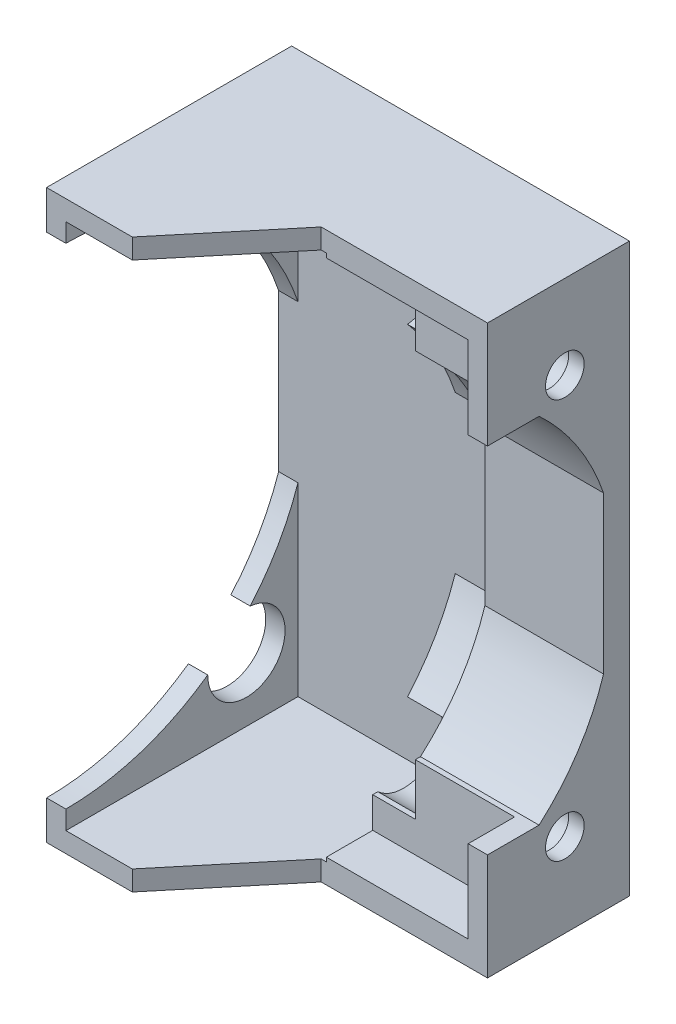
SolidWorks part; units mm, degrees
ref_plane "Alzado" through (0, 0, 0) normal (0, 0, 1) x (1, 0, 0)
ref_plane "Planta" through (0, 0, 0) normal (0, 1, 0) x (1, 0, 0)
ref_plane "Vista lateral" through (0, 0, 0) normal (1, 0, 0) x (0, 0, -1)
sketch "Croquis1" plane through (0, 0, 0) normal (0, 0, 1) x (1, 0, 0)
  line L1 (-34.6141, 8.9096) -> (-9.6141, 8.9096)
  line L2 (-34.6141, 8.9096) -> (-34.6141, -35.0904)
  line L3 (-34.6141, -35.0904) -> (-9.6141, -35.0904)
  line L4 (-9.6141, 8.9096) -> (-9.6141, -35.0904)
  dimension "D1" = 25
  dimension "D2" = 44
extrude "Saliente-Extruir1" add sketch "Croquis1" along normal blind 20
sketch "Croquis2" plane through (0, 0, 20) normal (0, 0, 1) x (1, 0, 0)
  line L0 (-34.6141, 8.9096) -> (-34.6141, -35.0904) construction
  line L1 (-32.6141, 7.1096) -> (-21.3141, 7.1096)
  line L2 (-32.6141, 7.1096) -> (-32.6141, -33.2904)
  line L3 (-32.6141, -33.2904) -> (-21.3141, -33.2904)
  line L4 (-21.3141, 7.1096) -> (-21.3141, -33.2904)
  line L5 (-9.6141, 8.9096) -> (-34.6141, 8.9096) construction
  dimension "D1" = 2
  dimension "D2" = 11.3
  dimension "D3" = 1.8
  dimension "D4" = 40.4
extrude "Cortar-Extruir1" cut sketch "Croquis2" against normal blind 18
sketch "Croquis3" plane through (0, 0, 20) normal (0, 0, 1) x (1, 0, 0)
  line L0 (-34.6141, -35.0904) -> (-9.6141, -35.0904) construction
  line L1 (-9.6141, 8.9096) -> (-20.3141, 8.9096)
  line L2 (-9.6141, 8.9096) -> (-9.6141, -35.0904)
  line L3 (-9.6141, -35.0904) -> (-20.3141, -35.0904)
  line L4 (-20.3141, 8.9096) -> (-20.3141, -35.0904)
  line L5 (-21.3141, -33.2904) -> (-21.3141, 7.1096) construction
  dimension "D1" = 1
extrude "Cortar-Extruir2" cut sketch "Croquis3" against normal blind 12
sketch "Croquis4" plane through (-34.6141, 0, 0) normal (-1, 0, 0) x (0, 0, 1)
  line L1 (20, 5.9096) -> (20, -32.0904)
  line L2 (0, 8.9096) -> (0, -35.0904) construction
  line L5 (20, 8.9096) -> (0, 8.9096) construction
  circle A0 centre (6, 2.4096) radius 1.6
  arc A1 (20, 5.9096) -> (20, -32.0904) centre (20, -13.0904) ccw
  circle A2 centre (6, -28.5904) radius 1.6
  dimension "D1" = 6
  dimension "D3" = 31
  dimension "D2" = 6.5
  dimension "D4" = 6
extrude "Cortar-Extruir3" cut sketch "Croquis4" against normal up to vertex
sketch "Croquis5" plane through (-34.6141, 0, 0) normal (-1, 0, 0) x (0, 0, 1)
  circle A0 centre (6, 2.4096) radius 3
  circle A1 centre (6, -28.5904) radius 3
extrude "Cortar-Extruir4" cut sketch "Croquis5" against normal blind 17
sketch "Croquis7" plane through (0, 0, 8) normal (0, 0, 1) x (1, 0, 0)
  line L0 (-20.3141, -30.8265) -> (-20.3141, -35.0904) construction
  line L1 (-9.6141, -35.0904) -> (-20.3141, -35.0904)
  line L2 (-9.6141, -35.0904) -> (-9.6141, -32.9585)
  line L3 (-9.6141, -32.9585) -> (-20.3141, -32.9585)
  line L4 (-20.3141, -35.0904) -> (-20.3141, -32.9585)
  line L5 (-20.3141, 8.9096) -> (-20.3141, 4.6456) construction
  line L6 (-9.6141, 8.9096) -> (-20.3141, 8.9096)
  line L7 (-9.6141, 8.9096) -> (-9.6141, 6.7776)
  line L8 (-9.6141, 6.7776) -> (-20.3141, 6.7776)
  line L9 (-20.3141, 8.9096) -> (-20.3141, 6.7776)
extrude "Saliente-Extruir2" add sketch "Croquis7" along normal up to vertex (12 mm away)
sketch "Croquis9" plane through (0, 0, 2) normal (0, 0, 1) x (1, 0, 0)
  line L1 (-21.3141, -7.0077) -> (-32.6141, -7.0077)
  line L2 (-21.3141, -7.0077) -> (-21.3141, -19.1732)
  line L3 (-21.3141, -19.1732) -> (-32.6141, -19.1732)
  line L4 (-32.6141, -7.0077) -> (-32.6141, -19.1732)
extrude "Saliente-Extruir3" add sketch "Croquis9" against normal up to vertex (2 mm away)
sketch "Croquis11" plane through (-32.6141, 0, 0) normal (-1, 0, 0) x (0, 0, 1)
  line L0 (2, -7.0077) -> (2, -19.1732)
  arc A0 (2, -7.0077) -> (2, -19.1732) centre (20, -13.0904) ccw
extrude "Saliente-Extruir4" add sketch "Croquis11" along normal up to vertex (2 mm away)
sketch "Croquis12" plane through (-34.6141, 0, 0) normal (-1, 0, 0) x (0, 0, 1)
  line L0 (20, -35.0904) -> (0, -35.0904) construction
  line L1 (0, 8.9096) -> (0.99, 8.9096)
  line L2 (0, 8.9096) -> (0, -35.0904)
  line L3 (0, -35.0904) -> (0.99, -35.0904)
  line L4 (0.99, 8.9096) -> (0.99, -35.0904)
  dimension "D1" = 0.99
extrude "Cortar-Extruir10" cut sketch "Croquis12" against normal up to vertex
sketch "Croquis13" plane through (-9.6141, 0, 0) normal (1, 0, 0) x (0, 0, -1)
  line L0 (-20, 8.9096) -> (-0.99, 8.9096) construction
  line L1 (-20, -35.0904) -> (-12, -35.0904)
  line L2 (-20, -35.0904) -> (-20, 8.9096)
  line L3 (-20, 8.9096) -> (-12, 8.9096)
  line L4 (-12, -35.0904) -> (-12, 8.9096)
  dimension "D1" = 8
extrude "Cortar-Extruir11" cut sketch "Croquis13" against normal up to vertex (11.7 mm away)
sketch "Croquis14" plane through (-21.3141, 0, 0) normal (1, 0, 0) x (0, 0, -1)
  line L0 (-2, -19.1732) -> (-2, -7.0077)
  arc A0 (-2, -19.1732) -> (-2, -7.0077) centre (-20, -13.0904) ccw
extrude "Saliente-Extruir5" add sketch "Croquis14" along normal up to vertex (11.7 mm away)
sketch "Croquis15" plane through (0, 0, 12) normal (0, 0, 1) x (1, 0, 0)
  line L1 (-9.6141, 6.7776) -> (-9.6141, 8.9096) construction
  line L2 (-20.3777, -33.4585) -> (-9.6141, -33.4585)
  line L3 (-20.3777, -33.4585) -> (-20.3777, 7.2776)
  line L4 (-20.3777, 7.2776) -> (-9.6141, 7.2776)
  line L8 (-9.6141, -33.4585) -> (-9.6141, 7.2776)
  line L9 (-20.3141, -32.9585) -> (-9.6141, -32.9585) construction
  line L10 (-9.6141, 6.7776) -> (-20.3141, 6.7776) construction
  dimension "D1" = 0.5
  dimension "D2" = 0.5
extrude "Cortar-Extruir12" cut sketch "Croquis15" against normal up to vertex (4 mm away)
sketch "Croquis16" plane through (-9.6141, 0, 0) normal (1, 0, 0) x (0, 0, -1)
  line L0 (-8, -27.8213) -> (-8, -33.4585)
  line L1 (-8, -33.4585) -> (-12, -33.4585)
  line L2 (-12, -33.4585) -> (-12, -35.0904)
  line L3 (-12, -35.0904) -> (-0.99, -35.0904)
  line L4 (-0.99, -35.0904) -> (-0.99, 8.9096)
  line L5 (-0.99, -35.0904) -> (-0.99, 8.9096) construction
  line L6 (-2, -7.0077) -> (-2, -19.1732)
  line L7 (-2, -7.0077) -> (-2, -19.1732) construction
  line L8 (-2, -13.0904) -> (-0.99, -13.0904) construction
  line L9 (-12, 8.9096) -> (-0.99, 8.9096)
  line L10 (-12, 7.2776) -> (-12, 8.9096)
  line L11 (-8, 7.2776) -> (-12, 7.2776)
  line L12 (-8, 1.6405) -> (-8, 7.2776)
  arc A0 (-8, -27.8213) -> (-2, -19.1732) centre (-20, -13.0904) ccw
  arc A1 (-8, 1.6405) -> (-2, -7.0077) centre (-20, -13.0904) cw
  circle A2 centre (-6, -28.5904) radius 1.5
  circle A3 centre (-6, 2.4096) radius 1.5
extrude "Saliente-Extruir6" add sketch "Croquis16" along normal blind 1.2
sketch "Croquis17" plane through (0, -35.0904, 0) normal (0, -1, 0) x (1, 0, 0)
  line L0 (-21.3141, 12) -> (-21.3141, 20)
  line L1 (-21.3141, 20) -> (-27.9641, 20)
  line L2 (-34.6141, 20) -> (-21.3141, 20) construction
  line L3 (-27.9641, 20) -> (-21.3141, 12)
extrude "Cortar-Extruir13" cut sketch "Croquis17" against normal up to vertex
sketch "Croquis18" plane through (0, 0, 12) normal (0, 0, 1) x (1, 0, 0)
  line L2 (-20.3777, 7.2776) -> (-21.3141, 7.2776)
  line L3 (-20.3777, 7.2776) -> (-20.3777, -33.2904)
  line L4 (-20.3777, -33.2904) -> (-21.3141, -33.2904)
  line L5 (-21.3141, 7.2776) -> (-21.3141, -33.2904)
extrude "Cortar-Extruir14" cut sketch "Croquis18" against normal up to vertex (4 mm away)
sketch "Croquis19" plane through (-8.4141, 0, 0) normal (1, 0, 0) x (0, 0, -1)
  line L0 (-2, -19.1732) -> (-2, -7.0077)
  line L1 (-8, -27.8213) -> (-8, -26.8213)
  line L2 (-8, 1.6405) -> (-8, 0.6405)
  line L3 (-3, -19.1732) -> (-3, -7.0077)
  arc A0 (-2, -19.1732) -> (-8, -27.8213) centre (-20, -13.0904) cw
  arc A1 (-2, -7.0077) -> (-8, 1.6405) centre (-20, -13.0904) ccw
  arc A2 (-8, -26.8213) -> (-3, -19.1732) centre (-19.1028, -14.1044) ccw
  arc A3 (-8, 0.6405) -> (-3, -7.0077) centre (-20.7177, -13.1322) cw
  dimension "D1" = 1
  dimension "D3" = 1
  dimension "D4" = 12.1655
  dimension "D5" = 1
extrude "Saliente-Extruir7" add sketch "Croquis19" against normal up to vertex
sketch "Croquis20" plane through (-8.4141, 0, 0) normal (1, 0, 0) x (0, 0, -1)
  line L1 (-8, -33.4585) -> (-12, -33.4585)
  line L2 (-8, -33.4585) -> (-8, -33.2224)
  line L3 (-8, -33.2224) -> (-12, -33.2224)
  line L4 (-12, -33.4585) -> (-12, -33.2224)
  line L5 (-8, 7.2776) -> (-12, 7.2776)
  line L6 (-8, 7.2776) -> (-8, 7.0276)
  line L7 (-8, 7.0276) -> (-12, 7.0276)
  line L8 (-12, 7.2776) -> (-12, 7.0276)
  dimension "D1" = 0.25
  dimension "D2" = 40.25
extrude "Saliente-Extruir8" add sketch "Croquis20" against normal up to vertex
sketch "Croquis21" plane through (-8.4141, 0, 0) normal (1, 0, 0) x (0, 0, -1)
  line L1 (-12, -33.2224) -> (-8, -33.2224)
  line L2 (-12, -33.2224) -> (-12, -26.8213)
  line L3 (-12, -26.8213) -> (-8, -26.8213)
  line L4 (-8, -33.2224) -> (-8, -26.8213)
  line L5 (-8, 0.6405) -> (-12, 0.6405)
  line L6 (-8, 0.6405) -> (-8, 7.0276)
  line L7 (-8, 7.0276) -> (-12, 7.0276)
  line L8 (-12, 0.6405) -> (-12, 7.0276)
extrude "Saliente-Extruir9" add sketch "Croquis21" against normal blind 1.5
sketch "Croquis22" plane through (0, 0, 8) normal (0, 0, 1) x (1, 0, 0)
  line L0 (-9.9141, 7.0276) -> (-21.3141, 7.0276)
  line L1 (-21.3141, 7.0276) -> (-21.3141, 4.6456)
  line L2 (-21.3141, 4.6456) -> (-17.6141, 4.6456)
  line L3 (-17.6141, 4.6456) -> (-17.6141, 0.6405)
  line L4 (-17.6141, 0.6405) -> (-9.9141, 0.6405)
  line L5 (-9.9141, 0.6405) -> (-9.9141, 7.0276)
  line L6 (-9.9141, -26.8213) -> (-17.6141, -26.8213)
  line L7 (-17.6141, -26.8213) -> (-17.6141, -30.8265)
  line L8 (-17.6141, -30.8265) -> (-21.3141, -30.8265)
  line L9 (-21.3141, -30.8265) -> (-21.3141, -33.2224)
  line L10 (-21.3141, -33.2224) -> (-9.9141, -33.2224)
  line L11 (-9.9141, -33.2224) -> (-9.9141, -26.8213)
extrude "Saliente-Extruir10" add sketch "Croquis22" along normal blind 0.4
sketch "Croquis23" plane through (0, 0, 20) normal (0, 0, 1) x (1, 0, 0)
  line L1 (-33.1141, 7.3596) -> (-20.9141, 7.3596)
  line L2 (-33.1141, 7.3596) -> (-33.1141, -33.5404)
  line L3 (-33.1141, -33.5404) -> (-20.9141, -33.5404)
  line L4 (-20.9141, 7.3596) -> (-20.9141, -33.5404)
  line L5 (-32.6141, 7.1096) -> (-32.6141, 5.9096) construction
  line L6 (-27.9641, 7.1096) -> (-32.6141, 7.1096) construction
  line L7 (-32.6141, -33.2904) -> (-27.9641, -33.2904) construction
  dimension "D1" = 0.5
  dimension "D2" = 0.25
  dimension "D3" = 0.25
  dimension "D4" = 12.2
extrude "Cortar-Extruir15" cut sketch "Croquis23" against normal up to vertex
